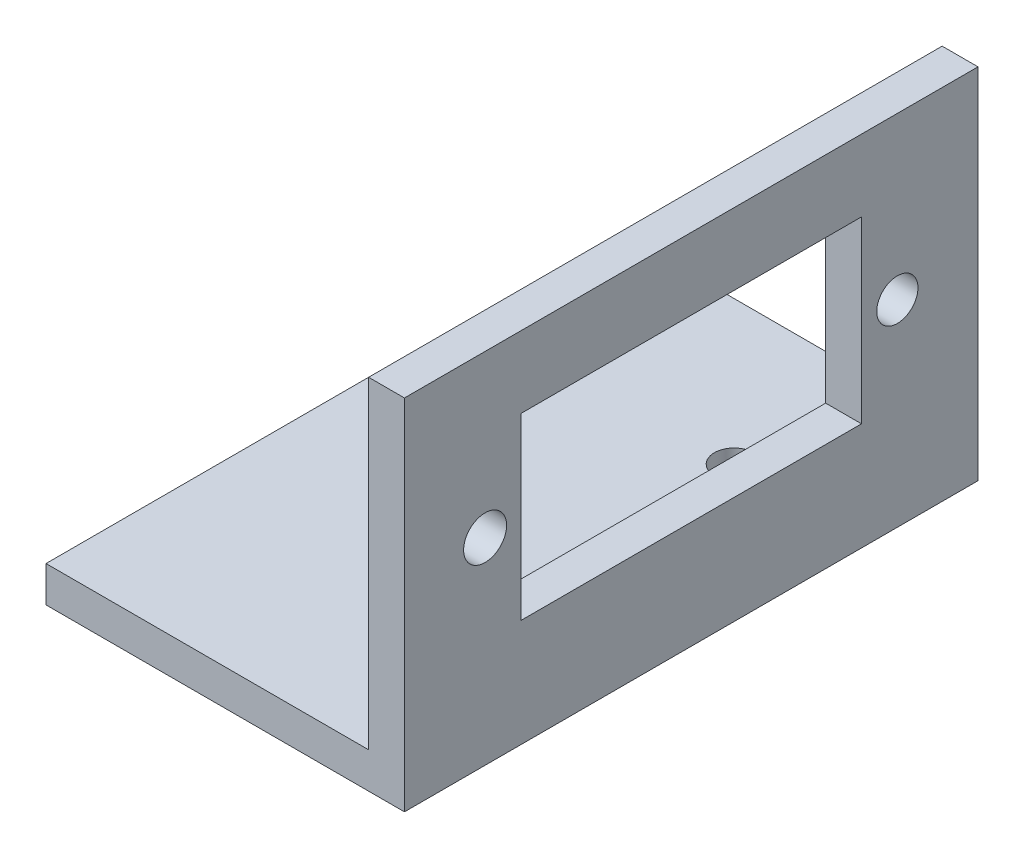
SolidWorks part; units mm, degrees
ref_plane "前视基准面" through (0, 0, 0) normal (0, 0, 1) x (1, 0, 0)
ref_plane "上视基准面" through (0, 0, 0) normal (0, 1, 0) x (1, 0, 0)
ref_plane "右视基准面" through (0, 0, 0) normal (1, 0, 0) x (0, 0, -1)
sketch "草图2" plane through (0, 0, 0) normal (0, 0, 1) x (1, 0, 0)
  line L0 (-20, 0) -> (0, 0)
  line L1 (0, 0) -> (0, 20)
  line L2 (0, 20) -> (-2, 20)
  line L3 (-2, 20) -> (-2, 2)
  line L4 (-2, 2) -> (-20, 2)
  line L5 (-20, 2) -> (-20, 0)
  dimension "D1" = 2
  dimension "D2" = 2
  dimension "D3" = 20
  dimension "D4" = 18
extrude "凸台-拉伸1" add sketch "草图2" along normal mid plane 32
sketch "草图4" plane through (0, 0, 0) normal (1, 0, 0) x (0, 0, -1)
  line L2 (-16, 20) -> (16, 20) construction
  line L3 (-9.5, 16) -> (9.5, 16)
  line L5 (-9.5, 16) -> (-9.5, 6)
  line L6 (-9.5, 6) -> (9.5, 6)
  line L7 (9.5, 16) -> (9.5, 6)
  circle A0 centre (11.5, 11) radius 1.15
  circle A1 centre (-11.5, 11) radius 1.2
  dimension "D1" = 2.4
  dimension "D2" = 5
  dimension "D3" = 23
  dimension "D4" = 9.5
  dimension "D9" = 5
  dimension "D6" = 11.5
  dimension "D5" = 19
  dimension "D7" = 4
  dimension "D8" = 10
extrude "切除-拉伸1" cut sketch "草图4" against normal blind 30
sketch "草图5" plane through (0, 2, 0) normal (0, 1, 0) x (1, 0, 0)
  circle A0 centre (-5.6098, 8) radius 1.1
  circle A1 centre (-5.6098, -8) radius 1.1
  dimension "D1" = 2.2
  dimension "D2" = 2.2
  dimension "D4" = 8
  dimension "D3" = 8
extrude "切除-拉伸2" cut sketch "草图5" against normal blind 30
